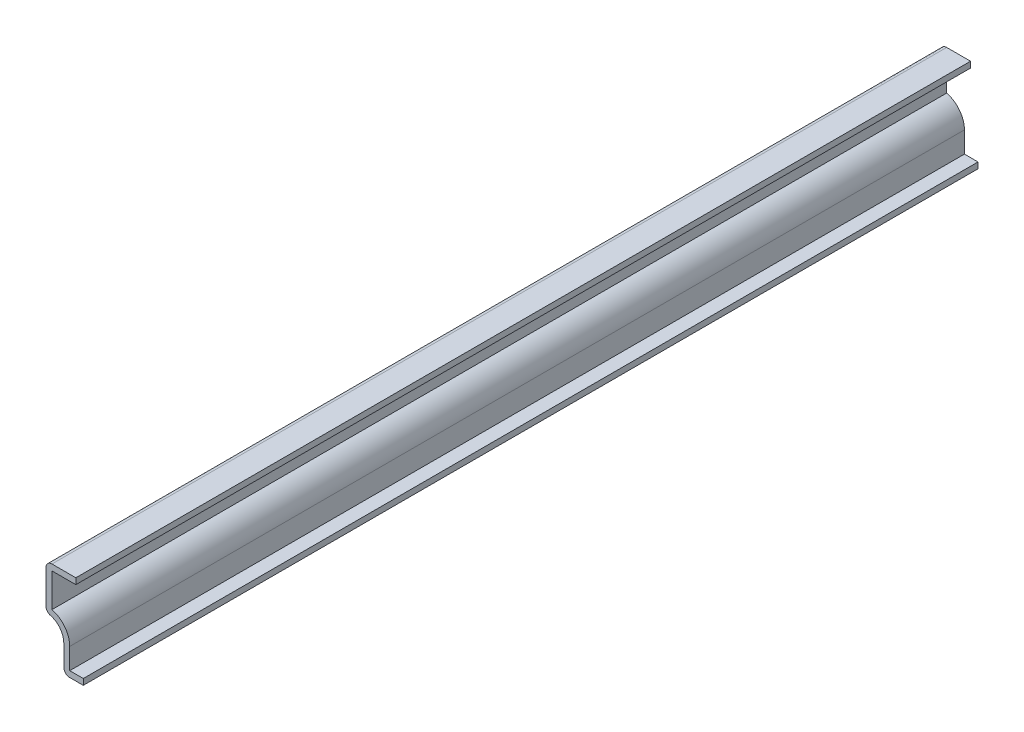
SolidWorks part; units mm, degrees
ref_plane "Front Plane" through (0, 0, 0) normal (0, 0, 1) x (1, 0, 0)
ref_plane "Top Plane" through (0, 0, 0) normal (0, 1, 0) x (1, 0, 0)
ref_plane "Right Plane" through (0, 0, 0) normal (1, 0, 0) x (0, 0, -1)
sketch "Sketch1" plane through (0, 0, 0) normal (0, 0, 1) x (1, 0, 0)
  line L0 (0, 0) -> (-4.155, 0)
  line L1 (-4.155, 0) -> (-4.155, 5.7425)
  line L2 (-7.9375, 9.525) -> (-7.9375, 19.05)
  line L3 (-7.9375, 19.05) -> (-1.5875, 19.05)
  line L4 (0, 0) -> (0, 19.05) construction
  line L5 (-12.9099, 0.0518) -> (-12.9099, 19.1018) construction
  arc A0 (-4.155, 5.7425) -> (-7.9375, 9.525) centre (-7.9375, 5.7425) ccw
  point P6 (-7.9375, 9.7308)
  dimension "D1" = 7.9375
  dimension "D2" = 19.05
  dimension "D3" = 19.05
  dimension "D4" = 4.155
  dimension "D5" = 9.525
  dimension "D6" = 6.35
extrude "Extrude-Thin1" add sketch "Sketch1" against normal blind 190.5 thin
fillet "Fillet1" radius 1.27 3 edges at (-4.155, 0, -95.25) (-7.9375, 9.525, -95.25) (-7.9375, 19.05, -95.25)
